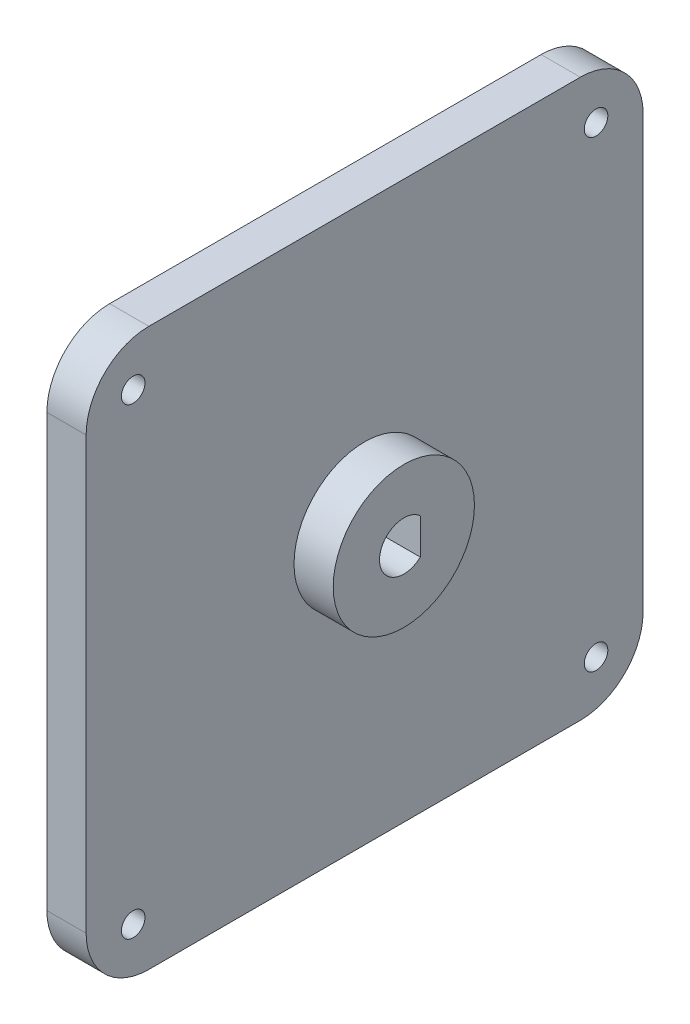
SolidWorks part; units mm, degrees
ref_plane "Front Plane" through (0, 0, 0) normal (0, 0, 1) x (1, 0, 0)
ref_plane "Top Plane" through (0, 0, 0) normal (0, 1, 0) x (1, 0, 0)
ref_plane "Right Plane" through (0, 0, 0) normal (1, 0, 0) x (0, 0, -1)
sketch "Sketch1" plane through (0, 0, 0) normal (1, 0, 0) x (0, 0, -1)
  line L1 (0, 0) -> (71, 0)
  line L2 (0, 0) -> (0, 71)
  line L3 (0, 71) -> (71, 71)
  line L4 (71, 0) -> (71, 71)
  circle A0 centre (6, 6) radius 1.5
  circle A1 centre (6, 65) radius 1.5
  circle A2 centre (65, 65) radius 1.5
  circle A3 centre (65, 6) radius 1.5
  dimension "D5" = 3
  dimension "D1" = 71
  dimension "D2" = 71
  dimension "D3" = 6
  dimension "D4" = 6
  dimension "D6" = 6
  dimension "D7" = 6
extrude "Boss-Extrude1" add sketch "Sketch1" along normal blind 5
fillet "Fillet1" radius 8 4 edges at (2.5, 0, 0) (2.5, 0, -71) (2.5, 71, -71) (2.5, 71, 0)
sketch "Sketch2" plane through (5, 0, 0) normal (1, 0, 0) x (0, 0, -1)
  line L1 (63, 71) -> (8, 71) construction
  line L2 (0, 63) -> (0, 8) construction
  circle A0 centre (35.5, 35.5) radius 9
  point P2 (35.5, 71)
  point P5 (0, 35.5)
  dimension "D1" = 18
  dimension "D2" = 35.5
  dimension "D3" = 35.5
extrude "Boss-Extrude2" add sketch "Sketch2" along normal blind 5
sketch "Sketch3" plane through (10, 0, 0) normal (1, 0, 0) x (0, 0, -1)
  line L1 (40.419, 39.6291) -> (37.6, 39.6291)
  line L2 (40.419, 39.6291) -> (40.419, 31.201)
  line L3 (40.419, 31.201) -> (37.6, 31.201)
  line L4 (37.6, 39.6291) -> (37.6, 31.201)
  circle A0 centre (35.5, 35.5) radius 3.1
  circle A1 centre (35.5, 35.5) radius 9 construction
  dimension "D1" = 6.2
  dimension "D2" = 2.1
extrude "Cut-Extrude1" cut sketch "Sketch3" against normal through all contours L4 A0
